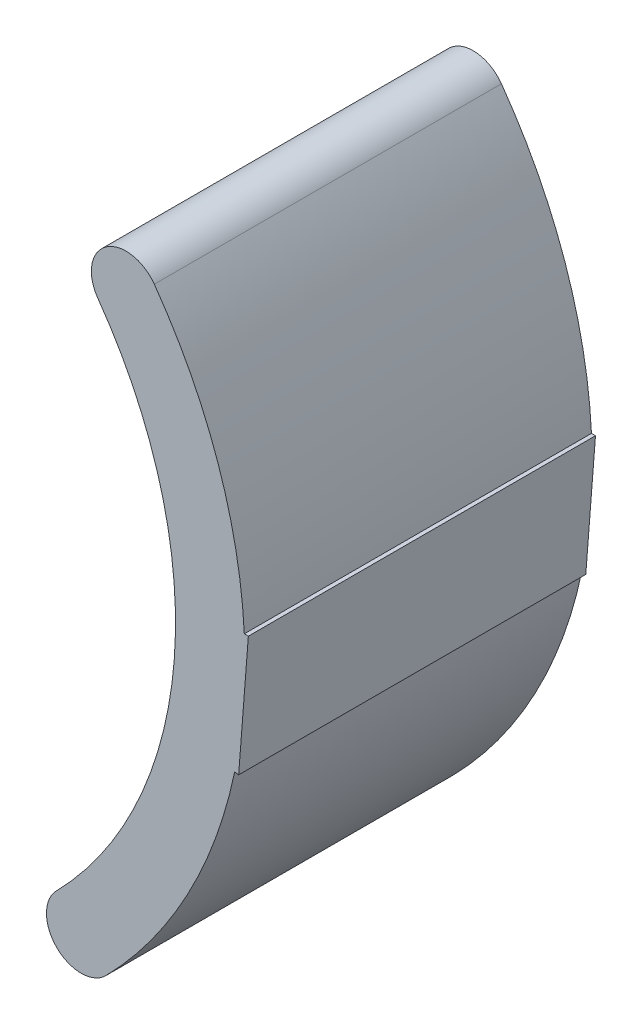
SolidWorks part; units mm, degrees
ref_plane "Plan de face" through (0, 0, 0) normal (0, 0, 1) x (1, 0, 0)
ref_plane "Plan de dessus" through (0, 0, 0) normal (0, 1, 0) x (1, 0, 0)
ref_plane "Plan de droite" through (0, 0, 0) normal (1, 0, 0) x (0, 0, -1)
sketch "Esquisse1" plane through (0, 0, 0) normal (0, 0, 1) x (1, 0, 0)
  line L0 (84.331, -6.5443) -> (0, 0) construction
  line L1 (84.331, -6.5443) -> (52.8763, 37.8035) construction
  line L2 (84.331, -6.5443) -> (46.411, -45.5084) construction
  line L3 (69.0917, -14.4159) -> (70.4886, 3.5841)
  line L4 (70.4886, 3.5841) -> (69.9082, 3.5841)
  line L5 (69.0917, -14.4159) -> (68.5183, -14.3264)
  arc A1 (42.8409, -42.0078) -> (48.8088, 34.8955) centre (0, 0) ccw
  arc A2 (49.9811, -49.0091) -> (68.5183, -14.3264) centre (0, 0) ccw
  arc A3 (42.8409, -42.0078) -> (49.9811, -49.0091) centre (46.411, -45.5084) ccw
  arc A4 (48.8088, 34.8955) -> (56.9437, 40.7114) centre (52.8763, 37.8035) cw
  arc A5 (69.9082, 3.5841) -> (56.9437, 40.7114) centre (0, 0) ccw
  arc A7 (49.9811, -49.0091) -> (56.9437, 40.7114) centre (0, 0) ccw construction
  point P17 (69.7902, -5.4159)
  dimension "D1" = 60
  dimension "D2" = 10
  dimension "D3" = 18
extrude "Boss.-Extru.1" add sketch "Esquisse1" along normal blind 50
